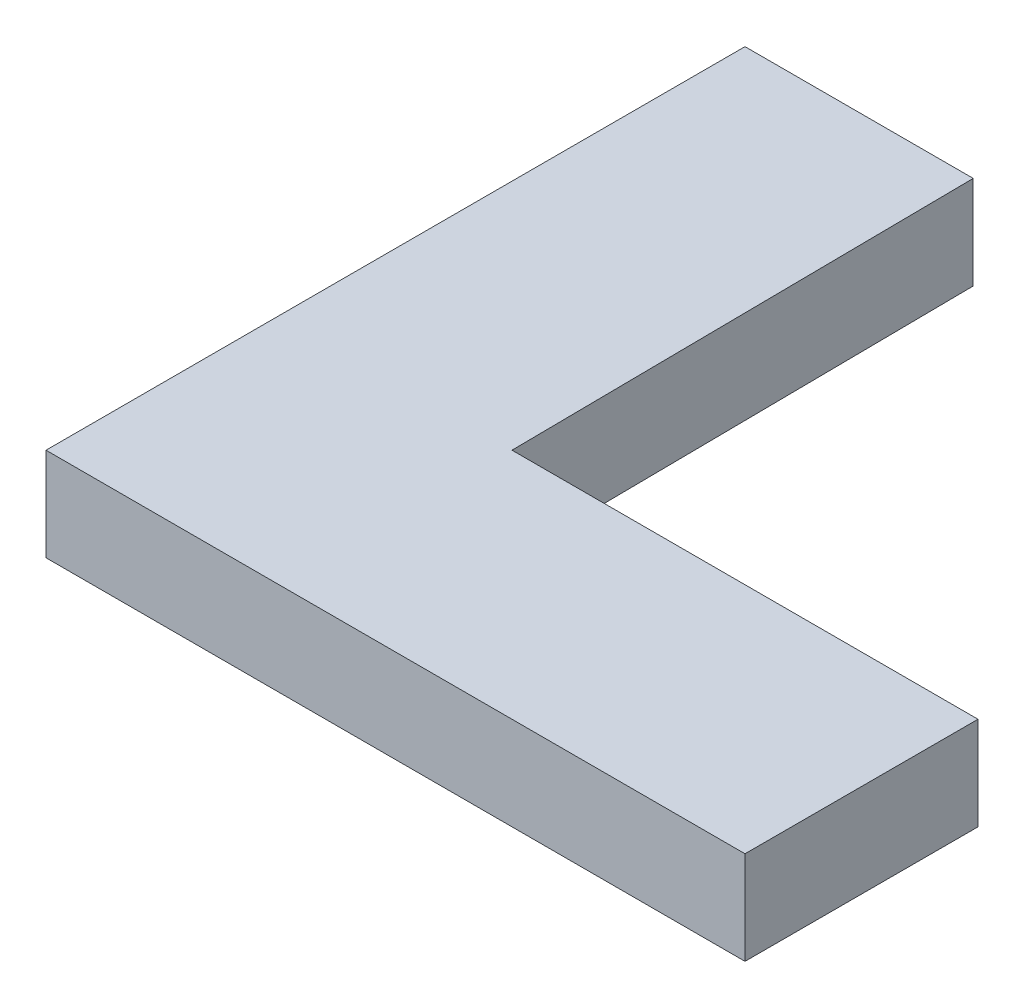
SolidWorks part; units mm, degrees
ref_plane "Front Plane" through (0, 0, 0) normal (0, 0, 1) x (1, 0, 0)
ref_plane "Top Plane" through (0, 0, 0) normal (0, 1, 0) x (1, 0, 0)
ref_plane "Right Plane" through (0, 0, 0) normal (1, 0, 0) x (0, 0, -1)
sketch "Sketch1" plane through (0, 0, 0) normal (0, 1, 0) x (1, 0, 0)
  line L0 (0, 0) -> (38.1, 0)
  line L1 (38.1, 0) -> (38.1, 12.7)
  line L2 (38.1, 12.7) -> (12.7, 12.7)
  line L3 (12.7, 12.7) -> (12.4396, 38.1)
  line L4 (12.4396, 38.1) -> (0, 38.1)
  line L5 (0, 38.1) -> (0, 0)
  dimension "D1" = 38.1
  dimension "D2" = 25.4
  dimension "D3" = 25.4
  dimension "D4" = 38.1
extrude "Boss-Extrude1" add sketch "Sketch1" along normal blind 5.08
